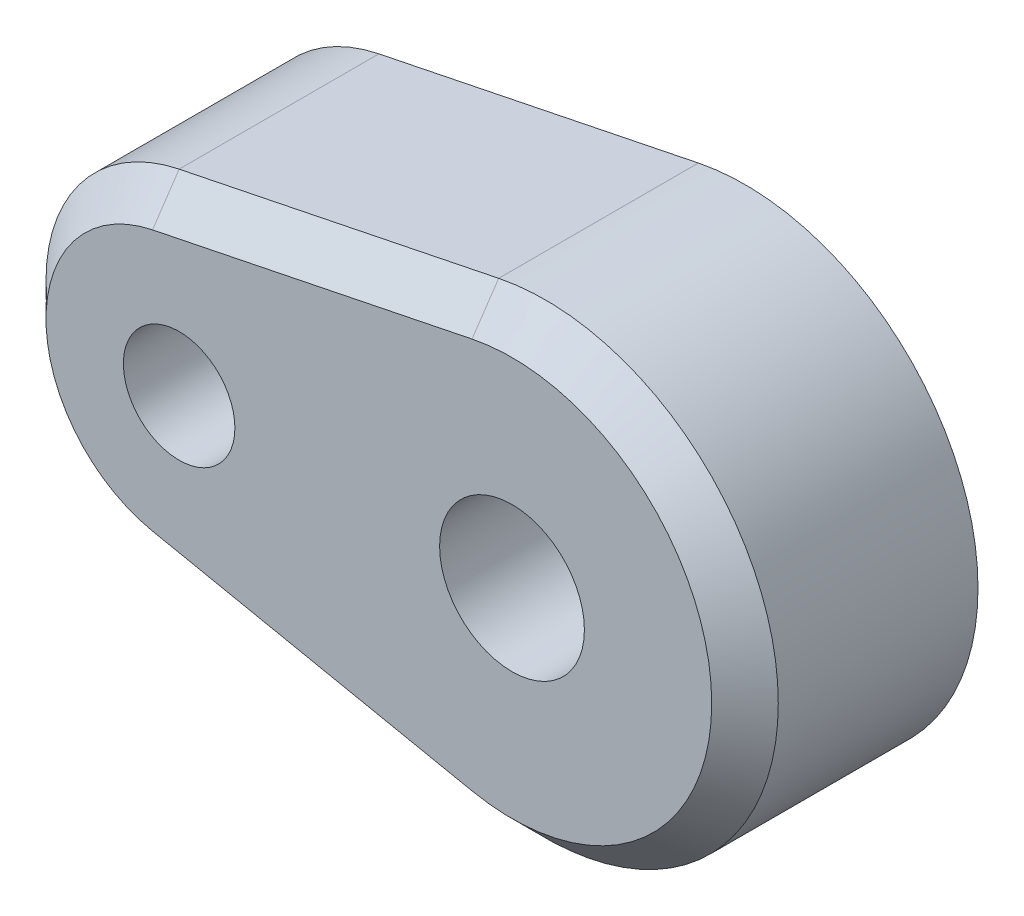
SolidWorks part; units mm, degrees
material "ABS"
ref_plane "Front Plane" through (0, 0, 0) normal (0, 0, 1) x (1, 0, 0)
ref_plane "Top Plane" through (0, 0, 0) normal (0, 1, 0) x (1, 0, 0)
ref_plane "Right Plane" through (0, 0, 0) normal (1, 0, 0) x (0, 0, -1)
sketch "Sketch1" plane through (0, 0, 0) normal (0, 0, 1) x (1, 0, 0)
  line L0 (0, 0) -> (-10, 0) construction
  line L1 (2.3094, -4) -> (4.6188, 0) construction
  line L2 (4.6188, 0) -> (2.3094, 4) construction
  line L3 (2.3094, 4) -> (-2.3094, 4) construction
  line L4 (-2.3094, 4) -> (-4.6188, 0) construction
  line L5 (-4.6188, 0) -> (-2.3094, -4) construction
  line L6 (-2.3094, -4) -> (2.3094, -4) construction
  line L7 (-1.4, 6.8586) -> (-11, 4.899)
  line L8 (-11, -4.899) -> (-1.4, -6.8586)
  circle A0 centre (0, 0) radius 2.175
  circle A1 centre (0, 0) radius 4 construction
  arc A2 (-1.4, -6.8586) -> (-1.4, 6.8586) centre (0, 0) ccw
  circle A3 centre (0, 0) radius 5 construction
  circle A4 centre (-10, 0) radius 1.675
  arc A5 (-11, 4.899) -> (-11, -4.899) centre (-10, 0) ccw
  dimension "D1" = 10
  dimension "D2" = 4.35
  dimension "D3" = 8
  dimension "D4" = 10
  dimension "D5" = 14
  dimension "D6" = 3.35
  dimension "D7" = 10
extrude "Boss-Extrude1" add sketch "Sketch1" along normal blind 7
sketch "Sketch2" plane through (0, 0, 0) normal (0, 0, -1) x (-1, 0, 0)
  circle A0 centre (0, 0) radius 5
  dimension "D1" = 10
extrude "Cut-Extrude1" cut sketch "Sketch2" against normal blind 3.4
chamfer "Chamfer1" distance 1 angle 45 4 edges at (-15, 0, 7) (-6.2, -5.8788, 7) (-6.2, 5.8788, 7) (7, 0, 7)
fillet "Fillet1" radius 0.5 2 edges at (-8.325, 0, 0) (-5, 0, 0)
